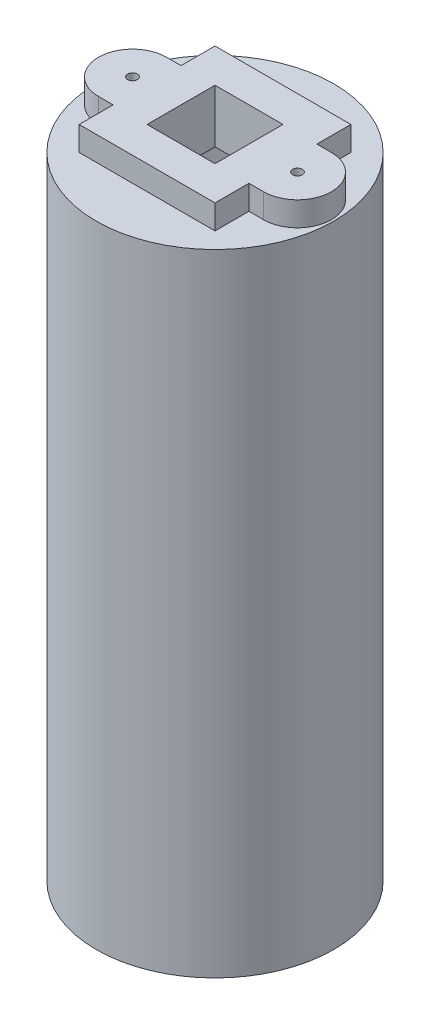
SolidWorks part; units mm, degrees
ref_plane "Front Plane" through (0, 0, 0) normal (0, 0, 1) x (1, 0, 0)
ref_plane "Top Plane" through (0, 0, 0) normal (0, 1, 0) x (1, 0, 0)
ref_plane "Right Plane" through (0, 0, 0) normal (1, 0, 0) x (0, 0, -1)
sketch "Sketch1" plane through (0, 0, 0) normal (0, 1, 0) x (1, 0, 0)
  circle A2 centre (0, 0) radius 12.25
  circle A3 centre (0, 0) radius 10.5
extrude "Boss-Extrude1" add sketch "Sketch1" along normal blind 62
sketch "Sketch2" plane through (0, 62, 0) normal (0, 1, 0) x (1, 0, 0)
  circle A0 centre (0, 0) radius 12.25
extrude "Boss-Extrude2" add sketch "Sketch2" along normal blind 3
sketch "Sketch8" plane through (0, 65, 0) normal (0, 1, 0) x (1, 0, 0)
  line L0 (-8.5, 0) -> (8.5, 0) construction
  line L1 (-7, 7) -> (7, 7)
  line L2 (-7, 7) -> (-7, -7)
  line L3 (-7, -7) -> (7, -7)
  line L4 (7, 7) -> (7, -7)
  line L5 (-7, 7) -> (7, -7) construction
  line L6 (-7, -7) -> (7, 7) construction
  line L7 (-8.5, 3.5) -> (8.5, 3.5)
  line L8 (-8.5, -3.5) -> (8.5, -3.5)
  arc A0 (-8.5, 3.5) -> (-8.5, -3.5) centre (-8.5, 0) ccw
  arc A1 (8.5, -3.5) -> (8.5, 3.5) centre (8.5, 0) ccw
  circle A2 centre (8.5, 0) radius 0.5
  circle A3 centre (-8.5, 0) radius 0.5
  point P0 (0, 0)
  point P8 (0, 0)
  dimension "D3" = 1
  dimension "D4" = 1
  dimension "D1" = 14
  dimension "D2" = 14
extrude "Boss-Extrude5" add sketch "Sketch8" along normal blind 2.5 contours L2 L7 L4 L1 | L2 L8 L4 L7 | L8 L2 L3 L4 | L7 A0 L8 L2 | L8 A1 L7 L4
sketch "Sketch9" plane through (0, 67.5, 0) normal (0, 1, 0) x (1, 0, 0)
  line L1 (-3.5, 3.5) -> (3.5, 3.5)
  line L2 (-3.5, 3.5) -> (-3.5, -3.5)
  line L3 (-3.5, -3.5) -> (3.5, -3.5)
  line L4 (3.5, 3.5) -> (3.5, -3.5)
  line L5 (-3.5, 3.5) -> (3.5, -3.5) construction
  line L6 (-3.5, -3.5) -> (3.5, 3.5) construction
  point P0 (0, 0)
  dimension "D1" = 7
  dimension "D2" = 7
extrude "Cut-Extrude3" cut sketch "Sketch9" against normal through all both and the other way through all
